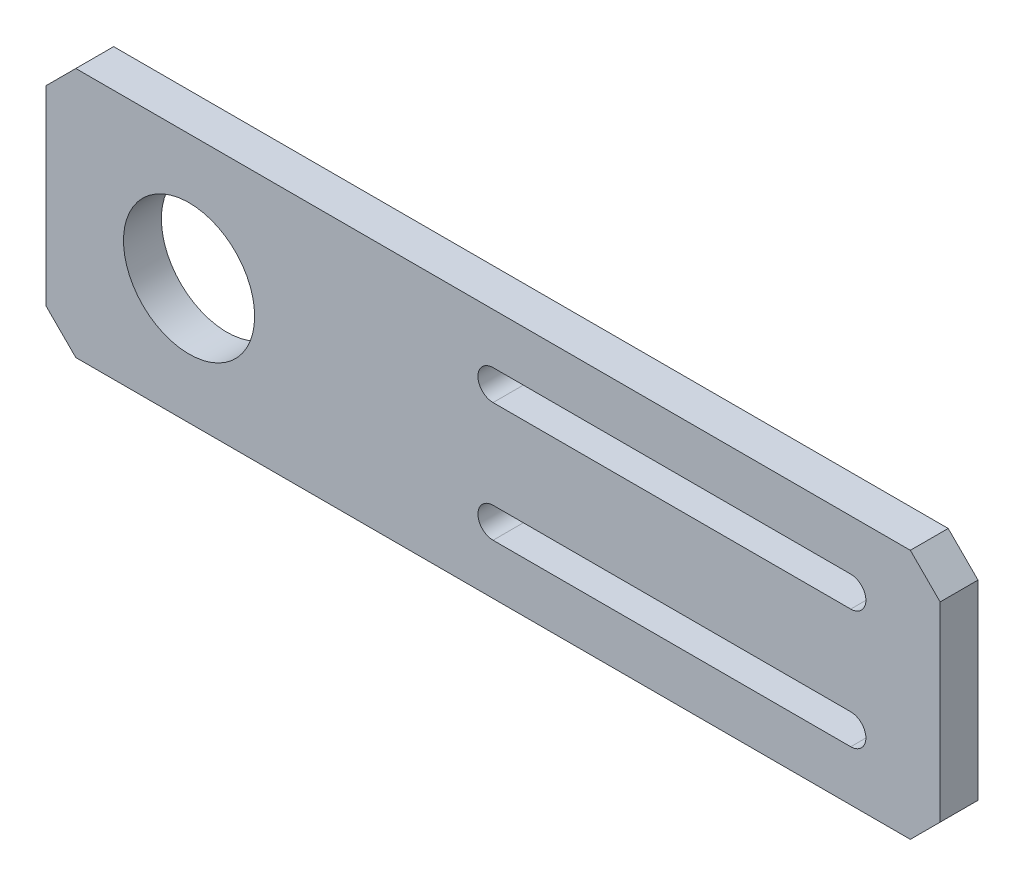
SolidWorks part; units mm, degrees
ref_plane "Front Plane" through (0, 0, 0) normal (0, 0, 1) x (1, 0, 0)
ref_plane "Top Plane" through (0, 0, 0) normal (0, 1, 0) x (1, 0, 0)
ref_plane "Right Plane" through (0, 0, 0) normal (1, 0, 0) x (0, 0, -1)
sketch "Sketch1" plane through (0, 0, 0) normal (0, 0, 1) x (1, 0, 0)
  line L1 (-102.5, 21) -> (102.5, 21)
  line L2 (-102.5, 21) -> (-102.5, -21)
  line L3 (-102.5, -21) -> (102.5, -21)
  line L4 (102.5, 21) -> (102.5, -21)
  line L5 (-102.5, 21) -> (102.5, -21) construction
  line L6 (-102.5, -21) -> (102.5, 21) construction
  point P0 (0, 0)
  dimension "D1" = 205
  dimension "D2" = 42
extrude "Boss-Extrude1" add sketch "Sketch1" along normal blind 6.35
sketch "Sketch3" plane through (0, 0, 6.35) normal (0, 0, 1) x (1, 0, 0)
  line L0 (-62.5, 10) -> (-62.5, -10) construction
  line L1 (-102.5, 21) -> (-102.5, -21) construction
  circle A0 centre (-62.5, 10) radius 2
  circle A1 centre (-62.5, -10) radius 2
  point P4 (-62.5, 0)
  dimension "D1" = 4
  dimension "D2" = 20
  dimension "D3" = 40
sketch "Sketch4" plane through (0, 0, 6.35) normal (0, 0, 1) x (1, 0, 0)
  line L0 (-102.5, 21) -> (-102.5, -21) construction
  line L1 (102.5, -21) -> (102.5, 21) construction
  circle A0 centre (-78.5, 0) radius 11
  circle A1 centre (82.5, 0) radius 11 construction
  dimension "D2" = 22
  dimension "D3" = 20
  dimension "D1" = 24
  dimension "D4" = 161
extrude "Cut-Extrude3" cut sketch "Sketch4" against normal through all
chamfer "Chamfer1" distance 5 angle 45 4 edges at (-102.5, 21, 3.175) (-102.5, -21, 3.175) (102.5, 21, 3.175) (102.5, -21, 3.175)
sketch "Sketch5" [suppressed] plane through (0, 0, 6.35) normal (0, 0, 1) x (1, 0, 0)
  line L0 (100, -16) -> (100, 16) construction
  circle A0 centre (77, 0) radius 11
  dimension "D1" = 22
  dimension "D2" = 23
extrude "Cut-Extrude4" [suppressed] cut sketch "Sketch5" against normal blind 25
sketch "Sketch8" plane through (0, 0, 6.35) normal (0, 0, 1) x (1, 0, 0)
  line L4 (25.5, 3.175) -> (10.5, 3.175)
  line L5 (10.5, 3.175) -> (10.5, -3.175)
  line L6 (10.5, -3.175) -> (25.5, -3.175)
  line L7 (25.5, -3.175) -> (25.5, 3.175)
  line L8 (25.5, 3.175) -> (10.5, 3.175)
  line L9 (10.5, 3.175) -> (10.5, -3.175)
  line L10 (10.5, -3.175) -> (25.5, -3.175)
  line L11 (25.5, -3.175) -> (25.5, 3.175)
  dimension "D1" = 0
extrude "Cut-Extrude7" [suppressed] cut sketch "Sketch8" against normal through all
sketch "Sketch9" plane through (0, 0, 6.35) normal (0, 0, 1) x (1, 0, 0)
  circle A0 centre (82.5, 0) radius 11 construction
  circle A1 centre (82.5, 0) radius 11
extrude "Cut-Extrude8" cut sketch "Sketch9" against normal through all
sketch "Sketch10" [suppressed] plane through (0, 0, 6.35) normal (0, 0, 1) x (1, 0, 0)
  circle A0 centre (80, 0) radius 15
  dimension "D1" = 25
extrude "Cut-Extrude9" [suppressed] cut sketch "Sketch10" against normal through all
sketch "Sketch11" plane through (0, 0, 6.35) normal (0, 0, 1) x (1, 0, 0)
  circle A0 centre (95.5563, 15.5563) radius 1.5 construction
  circle A1 centre (64.4437, 15.5563) radius 1.5 construction
  circle A2 centre (95.5563, -15.5563) radius 1.5 construction
  circle A3 centre (64.4437, -15.5563) radius 1.5 construction
  circle A4 centre (95.5563, 15.5563) radius 1.5
  circle A5 centre (64.4437, 15.5563) radius 1.5
  circle A6 centre (95.5563, -15.5563) radius 1.5
  circle A7 centre (64.4437, -15.5563) radius 1.5
sketch "Sketch12" plane through (0, 0, 6.35) normal (0, 0, 1) x (1, 0, 0)
  line L0 (-102.5, 16) -> (-102.5, -16) construction
  circle A0 centre (-95.5, 0) radius 3.302
  point P4 (-102.5, 0)
  dimension "D1" = 6.604
  dimension "D2" = 7
sketch "Sketch13" plane through (0, 0, 6.35) normal (0, 0, 1) x (1, 0, 0)
  line L0 (47.5, 16) -> (47.5, -16)
  line L1 (42.5, 21) -> (47.5, 16)
  line L2 (47.5, -16) -> (42.5, -21)
  line L3 (-97.5, -21) -> (97.5, -21) construction
  line L4 (97.5, 21) -> (-97.5, 21) construction
  line L5 (-97.5, -21) -> (97.5, -21)
  line L6 (97.5, 21) -> (-97.5, 21)
  line L7 (-27.5, 10) -> (32.5, 10) construction
  line L8 (97.5, 21) -> (-97.5, 21)
  line L9 (-97.5, 21) -> (-102.5, 16)
  line L10 (-102.5, 16) -> (-102.5, -16)
  line L11 (-102.5, -16) -> (-97.5, -21)
  line L12 (-97.5, -21) -> (97.5, -21)
  line L13 (97.5, -21) -> (102.5, -16)
  line L14 (102.5, -16) -> (102.5, 16)
  line L15 (102.5, 16) -> (97.5, 21)
  line L16 (42.5, 21) -> (-97.5, 21)
  line L17 (-97.5, 21) -> (-102.5, 16)
  line L18 (-102.5, 16) -> (-102.5, -16)
  line L19 (-102.5, -16) -> (-97.5, -21)
  line L20 (-97.5, -21) -> (42.5, -21)
  line L21 (97.5, -21) -> (102.5, -16)
  line L22 (102.5, -16) -> (102.5, 16)
  line L23 (102.5, 16) -> (97.5, 21)
  line L24 (-27.5, 12.54) -> (32.5, 12.54)
  line L25 (-27.5, 7.46) -> (32.5, 7.46)
  line L26 (0, 0) -> (47.5, 0) construction
  line L27 (-27.5, -10) -> (32.5, -10) construction
  line L28 (-27.5, -12.54) -> (32.5, -12.54)
  line L29 (-27.5, -7.46) -> (32.5, -7.46)
  arc A0 (-27.5, 12.54) -> (-27.5, 7.46) centre (-27.5, 10) ccw
  arc A1 (32.5, 7.46) -> (32.5, 12.54) centre (32.5, 10) ccw
  arc A2 (-27.5, -12.54) -> (-27.5, -7.46) centre (-27.5, -10) cw
  arc A3 (32.5, -7.46) -> (32.5, -12.54) centre (32.5, -10) cw
  point P2 (47.5, 21)
  point P9 (47.5, -21)
  point P16 (2.5, 10)
  point P27 (2.5, -10)
  circle M18 centre (82.5, 0) radius 11
  line M20 (97.5, 21) -> (-97.5, 21)
  line M24 (-97.5, -21) -> (97.5, -21)
  line M25 (97.5, -21) -> (102.5, -16)
  line M26 (102.5, -16) -> (102.5, 16)
  line M27 (102.5, 16) -> (97.5, 21)
  dimension "D3" = 2.54
  dimension "D2" = 150
  dimension "D4" = 60
  dimension "D7" = 15
  dimension "D8" = 10
  dimension "D1" = 0
extrude "Cut-Extrude10" cut sketch "Sketch13" against normal blind 10 contours L0 L2 L1 M24 M25 M26 M27 M20 M18 | L25 A1 L24 A0 | A3 L29 A2 L28
